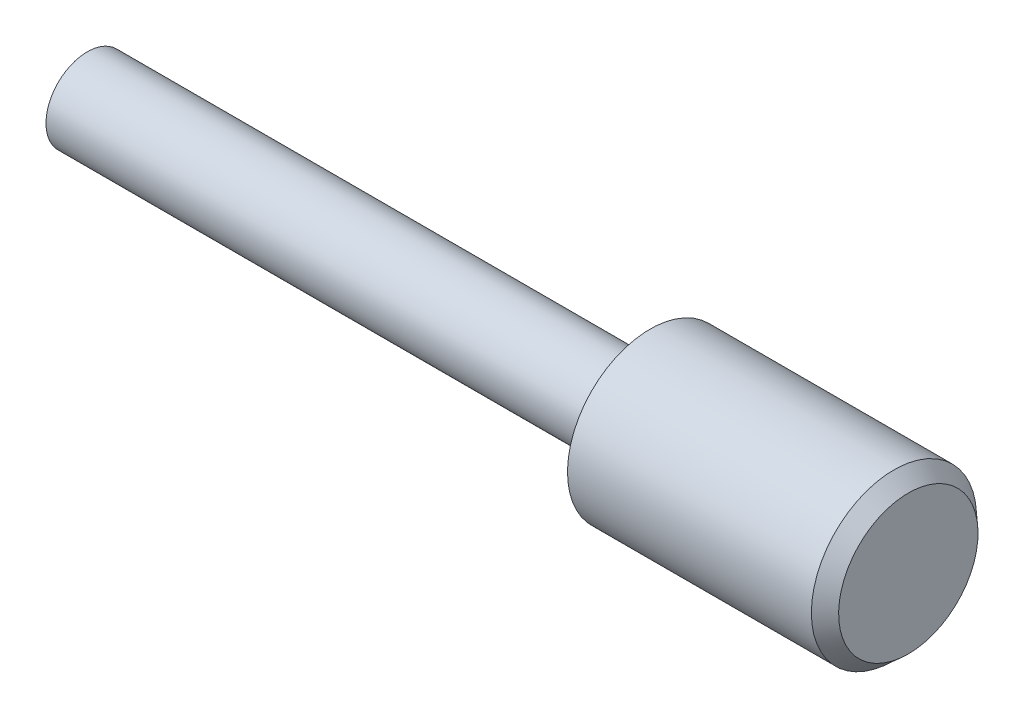
SolidWorks part; units mm, degrees
ref_plane "Ön Düzlem" through (0, 0, 0) normal (0, 0, 1) x (1, 0, 0)
ref_plane "Üst Düzlem" through (0, 0, 0) normal (0, 1, 0) x (1, 0, 0)
ref_plane "Sağ Düzlem" through (0, 0, 0) normal (1, 0, 0) x (0, 0, -1)
sketch "Çizim1" plane through (0, 0, 0) normal (0, 0, 1) x (1, 0, 0)
  line L0 (-218, -32) -> (100, -32)
  line L1 (0, 0) -> (100, 0)
  line L2 (0, 0) -> (0, -16)
  line L4 (100, 0) -> (100, -32)
  line L6 (-218, -32) -> (-218, -16)
  line L7 (-218, -16) -> (0, -16)
  dimension "D1" = 100
  dimension "D2" = 218
  dimension "D3" = 32
  dimension "D4" = 16
revolve "Döndür1" add sketch "Çizim1" angle 360 about L0
chamfer "Pah1" distance 5 angle 48 1 edges at (100, -64, 0)
